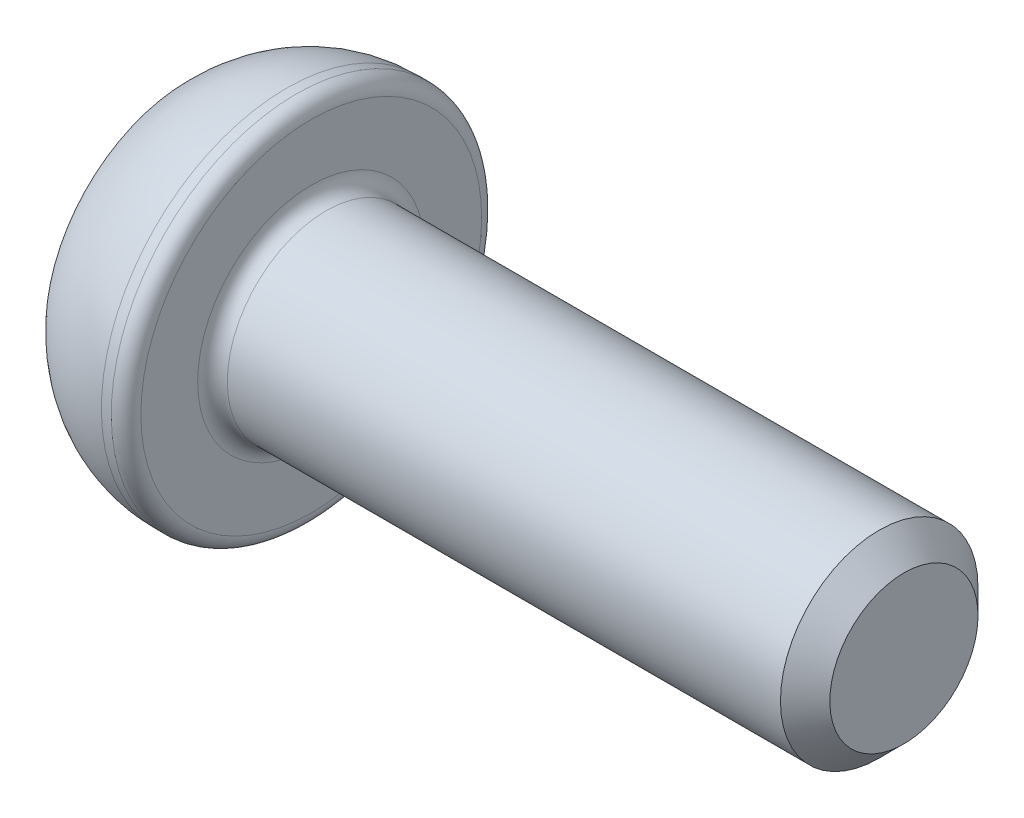
SolidWorks part; units mm, degrees
ref_plane "Спереди" through (0, 0, 0) normal (0, 0, 1) x (1, 0, 0)
ref_plane "Сверху" through (0, 0, 0) normal (0, 1, 0) x (1, 0, 0)
ref_plane "Справа" through (0, 0, 0) normal (1, 0, 0) x (0, 0, -1)
sketch "Эскиз1" plane through (0, 0, 0) normal (0, 0, 1) x (1, 0, 0)
  line L0 (0, 0) -> (0, 2.875)
  line L1 (2, 3.75) -> (2.5, 3.75)
  line L2 (2.5, 3.75) -> (2.5, 2)
  line L3 (2.5, 2) -> (14.5, 2)
  line L4 (14.5, 2) -> (14.5, 0)
  line L5 (14.5, 0) -> (0, 0) construction
  line L6 (0, 0) -> (14.5, 0)
  arc A0 (0, 2.875) -> (2, 3.75) centre (2, 1.0268) cw
  point P9 (2.5, 2.875)
  dimension "D1" = 0.5
  dimension "D2" = 4
  dimension "D3" = 7.5
  dimension "D5" = 2.5
  dimension "D6" = 12
revolve "Повернуть1" add sketch "Эскиз1" angle 360 about L5
cosmetic thread "Условное изображение резьбы1" parameters "D2"=3.22
sketch "Эскиз2" plane through (0, 0, 0) normal (-1, 0, 0) x (0, 0, 1)
  line L1 (0.7217, 1.25) -> (-0.7217, 1.25)
  line L2 (-0.7217, 1.25) -> (-1.4434, 0)
  line L3 (-1.4434, 0) -> (-0.7217, -1.25)
  line L4 (-0.7217, -1.25) -> (0.7217, -1.25)
  line L5 (0.7217, -1.25) -> (1.4434, 0)
  line L6 (1.4434, 0) -> (0.7217, 1.25)
  circle A0 centre (0, 0) radius 1.25 construction
  dimension "D1" = 2.5
extrude "Вырез-Вытянуть1" cut sketch "Эскиз2" against normal blind 1.5
fillet "Скругление1" radius 0.3 2 edges at (2.5, 2, 0) (2.5, 3.75, 0)
chamfer "Фаска1" distance 0.5 angle 45 1 edges at (14.5, 2, 0)
